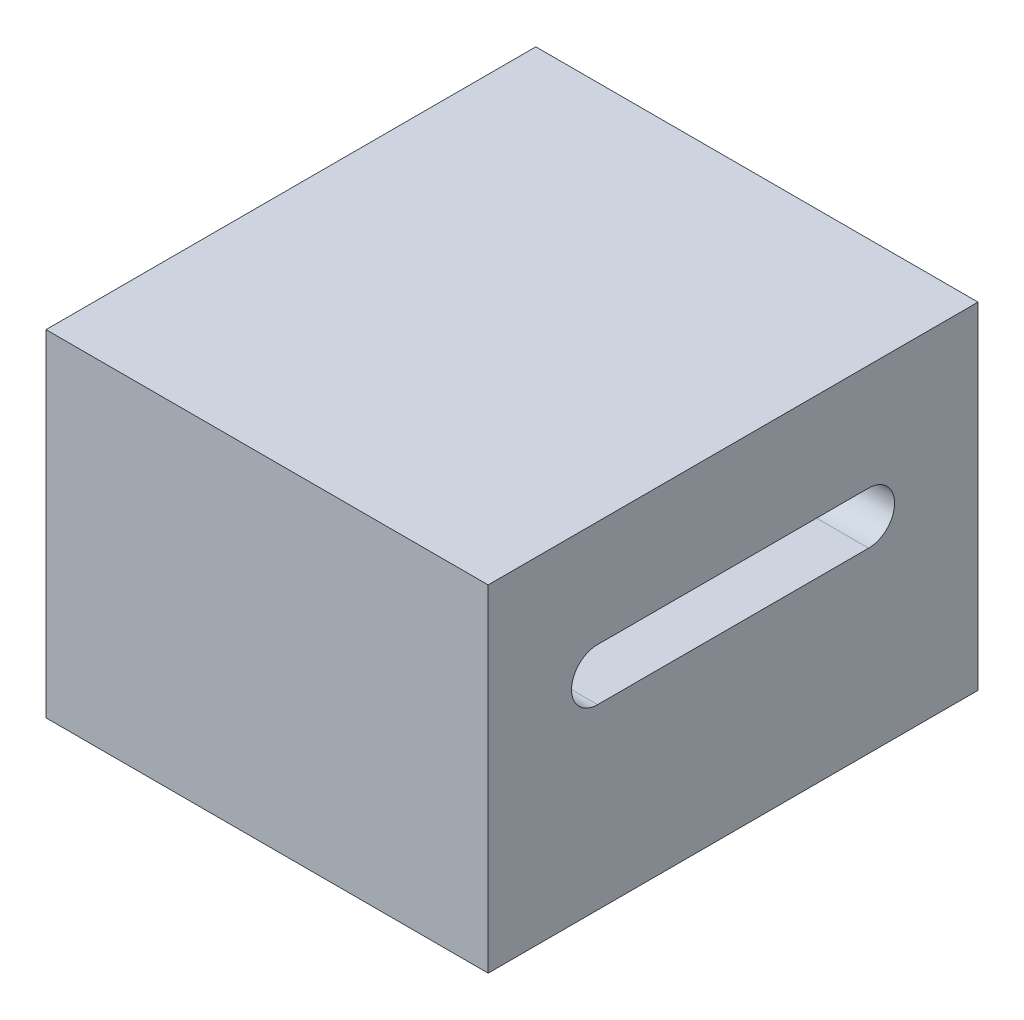
SolidWorks part; units mm, degrees
ref_plane "Front Plane" through (0, 0, 0) normal (0, 0, 1) x (1, 0, 0)
ref_plane "Top Plane" through (0, 0, 0) normal (0, 1, 0) x (1, 0, 0)
ref_plane "Right Plane" through (0, 0, 0) normal (1, 0, 0) x (0, 0, -1)
sketch "Sketch1" plane through (0, 0, 0) normal (0, 1, 0) x (1, 0, 0)
  line L1 (0, 0) -> (42.418, 0)
  line L2 (0, 0) -> (0, 46.99)
  line L3 (0, 46.99) -> (42.418, 46.99)
  line L4 (42.418, 0) -> (42.418, 46.99)
  dimension "D1" = 46.99
  dimension "D2" = 42.418
extrude "Boss-Extrude1" add sketch "Sketch1" along normal blind 32.258
sketch "Sketch2" plane through (42.418, 0, 0) normal (1, 0, 0) x (0, 0, -1)
  line L0 (10.495, 19.558) -> (36.495, 19.558) construction
  line L1 (10.495, 22.0541) -> (36.495, 22.0541)
  line L2 (10.495, 17.0619) -> (36.495, 17.0619)
  line L3 (0, 32.258) -> (46.99, 32.258) construction
  arc A0 (10.495, 22.0541) -> (10.495, 17.0619) centre (10.495, 19.558) ccw
  arc A1 (36.495, 17.0619) -> (36.495, 22.0541) centre (36.495, 19.558) ccw
  point P2 (23.495, 19.558)
  point P9 (0, 0)
  point P10 (23.495, 22.0541)
  point P11 (23.495, 32.258)
  dimension "D4" = 2.4961
  dimension "D1" = 12.7
  dimension "D2" = 26
extrude "Cut-Extrude1" cut sketch "Sketch2" against normal through all
